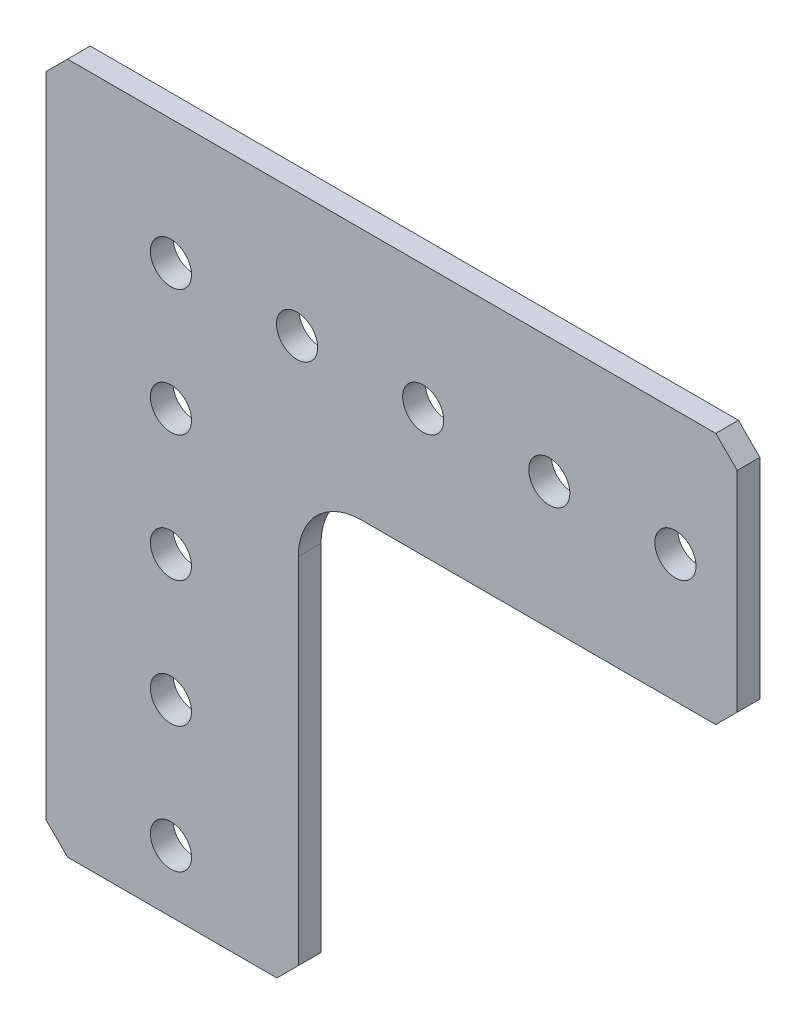
SolidWorks part; units mm, degrees
ref_plane "Front Plane" through (0, 0, 0) normal (0, 0, 1) x (1, 0, 0)
ref_plane "Top Plane" through (0, 0, 0) normal (0, 1, 0) x (1, 0, 0)
ref_plane "Right Plane" through (0, 0, 0) normal (1, 0, 0) x (0, 0, -1)
ref_plane "Plane1" through (0, 0, 0) normal (0, 0, -1) x (-1, 0, 0)
sketch "Sketch1" plane through (0, 0, 0) normal (0, 0, -1) x (-1, 0, 0)
  line L0 (10.414, 12.573) -> (-54.864, 12.573)
  line L1 (-54.864, 12.573) -> (-57.023, 10.414)
  line L2 (-57.023, 10.414) -> (-57.023, -10.668)
  line L3 (-57.023, -10.668) -> (-54.864, -12.827)
  line L4 (-54.864, -12.827) -> (-19.177, -12.827)
  line L5 (-12.827, -19.177) -> (-12.827, -54.864)
  line L6 (-12.827, -54.864) -> (-10.668, -57.023)
  line L7 (-10.668, -57.023) -> (10.414, -57.023)
  line L8 (10.414, -57.023) -> (12.573, -54.864)
  line L9 (12.573, -54.864) -> (12.573, 10.414)
  line L10 (12.573, 10.414) -> (10.414, 12.573)
  arc A0 (-19.177, -12.827) -> (-12.827, -19.177) centre (-19.177, -19.177) cw
  circle A1 centre (0, -50.8) radius 2.0701
  circle A2 centre (0, -25.4) radius 2.0701
  circle A3 centre (-38.1, 0) radius 2.0701
  circle A4 centre (-12.7, 0) radius 2.0701
  circle A5 centre (0, 0) radius 2.0701
  circle A6 centre (-25.4, 0) radius 2.0701
  circle A7 centre (0, -12.7) radius 2.0701
  circle A8 centre (0, -38.1) radius 2.0701
  circle A9 centre (-50.8, 0) radius 2.0701
extrude "Boss-Extrude1" add sketch "Sketch1" against normal blind 2.286
